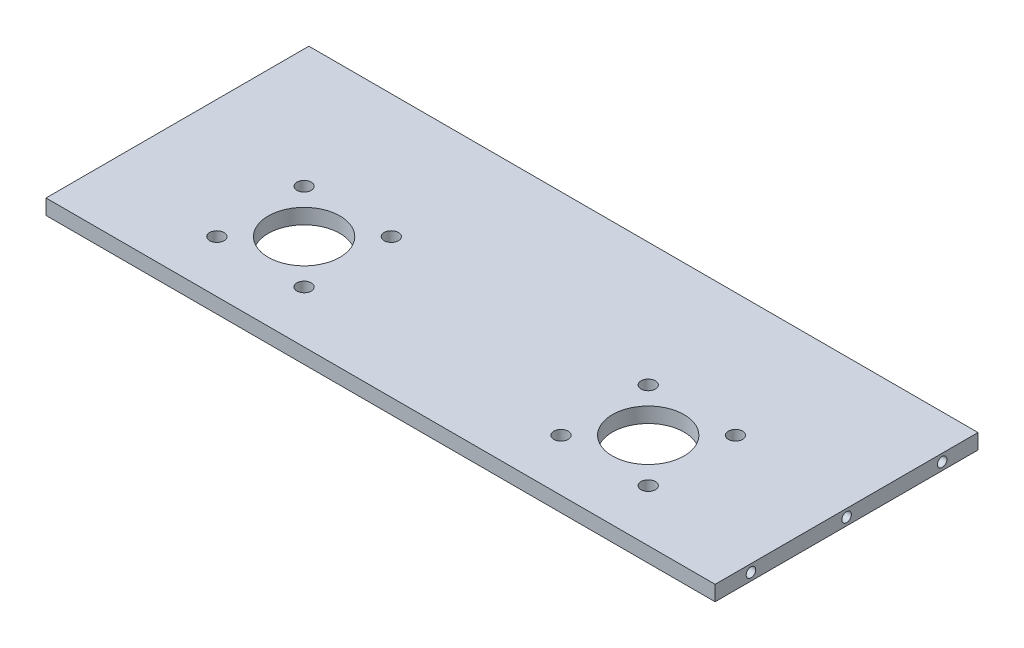
SolidWorks part; units mm, degrees
ref_plane "Alzado" through (0, 0, 0) normal (0, 0, 1) x (1, 0, 0)
ref_plane "Planta" through (0, 0, 0) normal (0, 1, 0) x (1, 0, 0)
ref_plane "Vista lateral" through (0, 0, 0) normal (1, 0, 0) x (0, 0, -1)
sketch "Croquis1" plane through (0, 0, 0) normal (0, 1, 0) x (1, 0, 0)
  line L1 (-125.7057, 56.7568) -> (154.2943, 56.7568)
  line L2 (-125.7057, 56.7568) -> (-125.7057, -53.2432)
  line L3 (-125.7057, -53.2432) -> (154.2943, -53.2432)
  line L4 (154.2943, 56.7568) -> (154.2943, -53.2432)
  dimension "D1" = 280
  dimension "D2" = 110
extrude "Saliente-Extruir1" add sketch "Croquis1" along normal blind 6.35
sketch "Croquis2" plane through (0, 0, 0) normal (0, 1, 0) x (1, 0, 0)
  line L0 (-125.7057, 56.7568) -> (-125.7057, -53.2432) construction
  line L5 (14.2943, -3.2432) -> (14.2943, 86.0992) construction
  line L6 (14.2943, 86.0992) -> (14.2943, -88.1745) construction
  circle A0 centre (-39.4557, 5.0068) radius 3
  circle A1 centre (-75.9557, 5.0068) radius 3
  circle A2 centre (86.2943, -13.2432) radius 15
  circle A3 centre (-57.7057, -13.2432) radius 15
  circle A4 centre (-39.4557, -31.4932) radius 3
  circle A5 centre (-75.9557, -31.4932) radius 3
  circle A6 centre (104.5443, 5.0068) radius 3
  circle A7 centre (68.0443, 5.0068) radius 3
  circle A8 centre (104.5443, -31.4932) radius 3
  circle A9 centre (68.0443, -31.4932) radius 3
  point P4 (0, 0)
  point P28 (66.2339, 2.5278)
  dimension "D4" = 6
  dimension "D5" = 30
  dimension "D6" = 30
  dimension "D9" = 6
  dimension "D1" = 36.5
  dimension "D2" = 144
  dimension "D3" = 36.5
  dimension "D7" = 72
  dimension "D8" = 72
  dimension "D10" = 36.5
  dimension "D11" = 18.25
  dimension "D12" = 18.25
  dimension "D13" = 36.5
  dimension "D14" = 140
  dimension "D15" = 36.5
  dimension "D16" = 36.5
  dimension "D17" = 36.5
  dimension "D18" = 36.5
extrude "Cortar-Extruir2" cut sketch "Croquis2" along normal blind 20
sketch "Croquis5" plane through (-125.7057, 0, 0) normal (-1, 0, 0) x (0, 0, 1)
  line L0 (53.2432, 6.35) -> (53.2432, 0) construction
  line L2 (-56.7568, 6.35) -> (-56.7568, 0) construction
  line L4 (-56.7568, 3.175) -> (53.2432, 3.175) construction
  circle A0 centre (38.2432, 3.175) radius 2
  circle A1 centre (-41.7568, 3.175) radius 2
  circle A2 centre (-1.7568, 3.175) radius 2
  dimension "D3" = 4
  dimension "D6" = 4
  dimension "D2" = 4
  dimension "D1" = 15
  dimension "D4" = 15
  dimension "D5" = 40
  dimension "D7" = 40
extrude "Cortar-Extruir5" cut sketch "Croquis5" against normal blind 30
sketch "Croquis6" plane through (154.2943, 0, 0) normal (1, 0, 0) x (0, 0, -1)
  line L1 (-53.2432, 6.35) -> (-53.2432, 0) construction
  line L2 (56.7568, 6.35) -> (56.7568, 0) construction
  line L3 (-53.2432, 3.175) -> (56.7568, 3.175) construction
  circle A0 centre (41.7568, 3.175) radius 2
  circle A1 centre (-38.2432, 3.175) radius 2
  circle A2 centre (1.7568, 3.175) radius 2
  dimension "D1" = 4
  dimension "D2" = 4
  dimension "D3" = 4
  dimension "D4" = 40
  dimension "D5" = 15
  dimension "D6" = 15
  dimension "D7" = 40
extrude "Cortar-Extruir6" cut sketch "Croquis6" against normal blind 30
